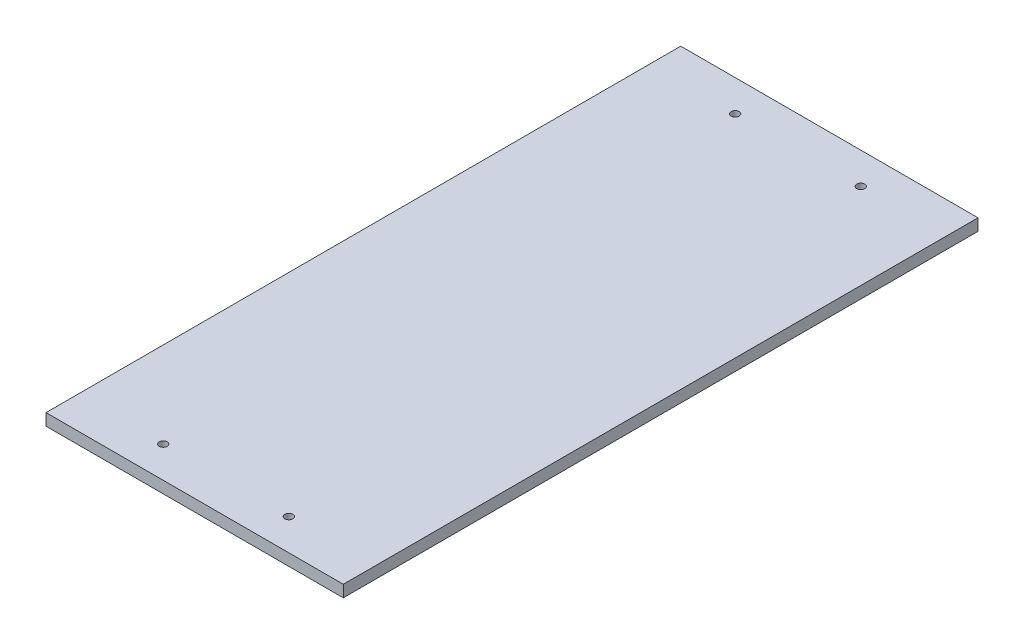
SolidWorks part; units mm, degrees
material "Balsa"
ref_plane "Front Plane" through (0, 0, 0) normal (0, 0, 1) x (1, 0, 0)
ref_plane "Top Plane" through (0, 0, 0) normal (0, 1, 0) x (1, 0, 0)
ref_plane "Right Plane" through (0, 0, 0) normal (1, 0, 0) x (0, 0, -1)
sketch "Sketch1" plane through (0, 0, 0) normal (0, 1, 0) x (1, 0, 0)
  line L0 (-152.4, 304.8) -> (152.4, 304.8) construction
  line L1 (152.4, 304.8) -> (152.4, -304.8) construction
  line L2 (0, 304.8) -> (0, 0) construction
  line L3 (0, 0) -> (152.4, 0) construction
  dimension "Width" = 304.8
  dimension "Length" = 609.6
sketch "Sketch2" plane through (0, 0, 0) normal (1, 0, 0) x (0, 0, -1)
  line L0 (304.8, 0) -> (304.8, -9.525) construction
  dimension "Thk" = 9.525
sketch "Sketch3" plane through (0, 0, 0) normal (0, 1, 0) x (1, 0, 0)
  line L1 (-152.4, 304.8) -> (152.4, 304.8)
  line L2 (-152.4, 304.8) -> (-152.4, -304.8)
  line L3 (-152.4, -304.8) -> (152.4, -304.8)
  line L4 (152.4, 304.8) -> (152.4, -304.8)
extrude "Boss-Extrude1" add sketch "Sketch3" against normal up to vertex (9.525 mm away) up to point (0, -9.525, -304.8)
sketch "Sketch4" plane through (0, 0, 0) normal (0, 1, 0) x (1, 0, 0)
  line L0 (152.4, -304.8) -> (152.4, 304.8) construction
  line L1 (-152.4, 304.8) -> (152.4, 304.8)
  line L2 (-152.4, 304.8) -> (-152.4, 208.661)
  line L3 (-120.245, 208.661) -> (120.245, 208.661)
  line L4 (152.4, 304.8) -> (152.4, 208.661)
  line L5 (-152.4, -304.8) -> (152.4, -304.8) construction
  line L6 (0, 0) -> (0, 208.661) construction
  line L8 (-152.4, 208.661) -> (-152.4, -304.8)
  line L9 (-152.4, -304.8) -> (-120.245, -304.8)
  line L10 (-120.245, 208.661) -> (-120.245, -304.8)
  line L11 (152.4, 208.661) -> (152.4, -304.8)
  line L12 (120.245, 208.661) -> (120.245, -304.8)
  line L13 (152.4, -304.8) -> (120.245, -304.8)
  dimension "D1" = 513.461
  dimension "D2" = 32.155
  dimension "D3" = 32.155
extrude "Cut-Extrude1" cut sketch "Sketch4" against normal blind 15.24 contours L2 L8 L9 L10 L3 L12 L13 L11 L4 L1
sketch "Sketch5" plane through (0, 0, 0) normal (0, 1, 0) x (1, 0, 0)
  line L1 (-50.8, -109.22) -> (50.8, -109.22)
  line L2 (-57.15, -102.87) -> (-57.15, -20.32)
  line L3 (-50.8, -13.97) -> (50.8, -13.97)
  line L4 (57.15, -102.87) -> (57.15, -20.32)
  line L5 (-57.15, -109.22) -> (57.15, -13.97) construction
  line L6 (-57.15, -13.97) -> (57.15, -109.22) construction
  arc A0 (-50.8, -109.22) -> (-57.15, -102.87) centre (-50.8, -102.87) cw
  arc A1 (50.8, -109.22) -> (57.15, -102.87) centre (50.8, -102.87) ccw
  arc A2 (50.8, -13.97) -> (57.15, -20.32) centre (50.8, -20.32) cw
  arc A3 (-57.15, -20.32) -> (-50.8, -13.97) centre (-50.8, -20.32) cw
  point P0 (0, -61.595)
  dimension "D4" = 6.35
  dimension "D1" = 95.25
  dimension "D2" = 61.595
  dimension "D3" = 114.3
extrude "Cut-Extrude2" [suppressed] cut sketch "Sketch5" against normal blind 12.7
sketch "Sketch9" plane through (0, -9.525, 0) normal (0, -1, 0) x (-1, 0, 0)
  line L0 (120.245, 208.661) -> (-120.245, 208.661) construction
  line L1 (120.245, 208.661) -> (-120.245, 208.661) construction
  line L2 (0, 208.661) -> (0, 0) construction
  line L3 (-120.245, 208.661) -> (-120.245, -304.8) construction
  line L4 (120.245, -304.8) -> (-120.245, -304.8) construction
  line L5 (-120.245, -304.8) -> (-120.245, -48.0695) construction
  line L6 (-120.245, -48.0695) -> (120.245, -48.0695) construction
  line L7 (50.8, 208.661) -> (0, 208.661) construction
  line L8 (0, 208.661) -> (-50.8, 208.661) construction
  line L9 (50.8, 208.661) -> (50.8, 183.261) construction
  line L10 (50.8, 183.261) -> (-50.8, 183.261) construction
  line L11 (-50.8, 183.261) -> (-50.8, 208.661) construction
  line L13 (120.245, 208.661) -> (120.245, -304.8) construction
  line L14 (-120.245, 208.661) -> (-120.245, -304.8) construction
  circle A0 centre (-50.8, 183.261) radius 3.2258
  circle A2 centre (50.8, 183.261) radius 3.2258
  circle A5 centre (50.8, -279.4) radius 3.2258
  circle A6 centre (-50.8, -279.4) radius 3.2258
  point P17 (0, 0)
  point P23 (120.245, -48.0695)
  point P26 (-81.6356, -48.0695)
  point P29 (0, 0)
  point P30 (-120.245, 208.661)
  point P31 (0, 0)
  point P32 (0, 0)
  point P34 (0, 0)
  dimension "D3" = 25.4
  dimension "D1" = 6.4516
  dimension "D2" = 50.8
  dimension "D4" = 50.8
extrude "Cut-Extrude3" cut sketch "Sketch9" against normal through all
